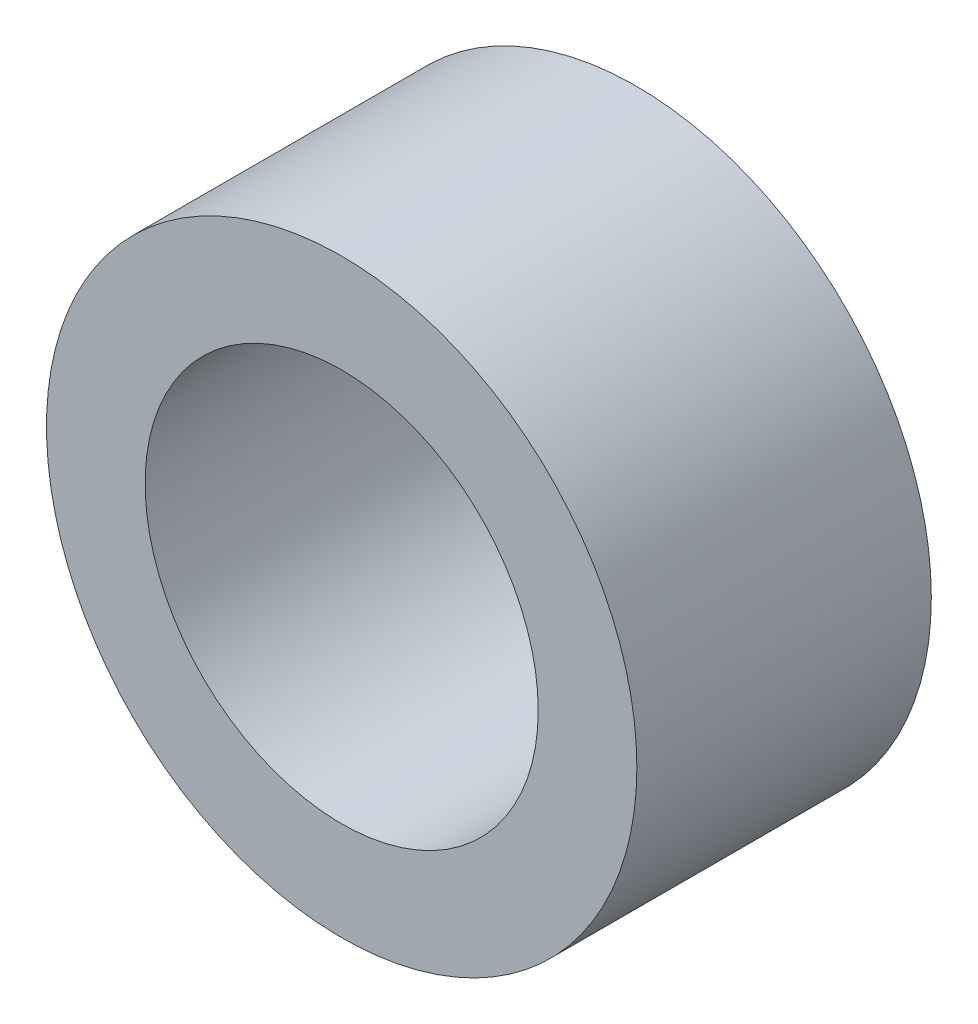
SolidWorks part; units mm, degrees
material "Brass"
ref_plane "Front Plane" through (0, 0, 0) normal (0, 0, 1) x (1, 0, 0)
ref_plane "Top Plane" through (0, 0, 0) normal (0, 1, 0) x (1, 0, 0)
ref_plane "Right Plane" through (0, 0, 0) normal (1, 0, 0) x (0, 0, -1)
sketch "Sketch1" plane through (0, 0, 0) normal (0, 0, 1) x (1, 0, 0)
  circle A0 centre (0, 0) radius 6.015
  circle A1 centre (0, 0) radius 4.005
  dimension "D1" = 12.03
  dimension "ID" = 8.01
extrude "Extrude1" add sketch "Sketch1" along normal mid plane 6
sketch "Sketch2" plane through (0, 0, 0) normal (1, 0, 0) x (0, 0, -1)
  line L0 (-3, -4.005) -> (3, -4.005) construction
  line L3 (3, 4.005) -> (-3, 4.005) construction
  line L5 (-3, -4.005) -> (3, -4.005)
  line L6 (3, 4.005) -> (-3, 4.005)
sketch "Sketch4" plane through (0, 0, 3) normal (0, 0, 1) x (1, 0, 0)
  line L0 (0, 0) -> (-2.832, 2.832)
  line L1 (0, -5.5) -> (0, 5.5) construction
  circle A0 centre (0, 0) radius 4.005 construction
  dimension "D1" = 45
